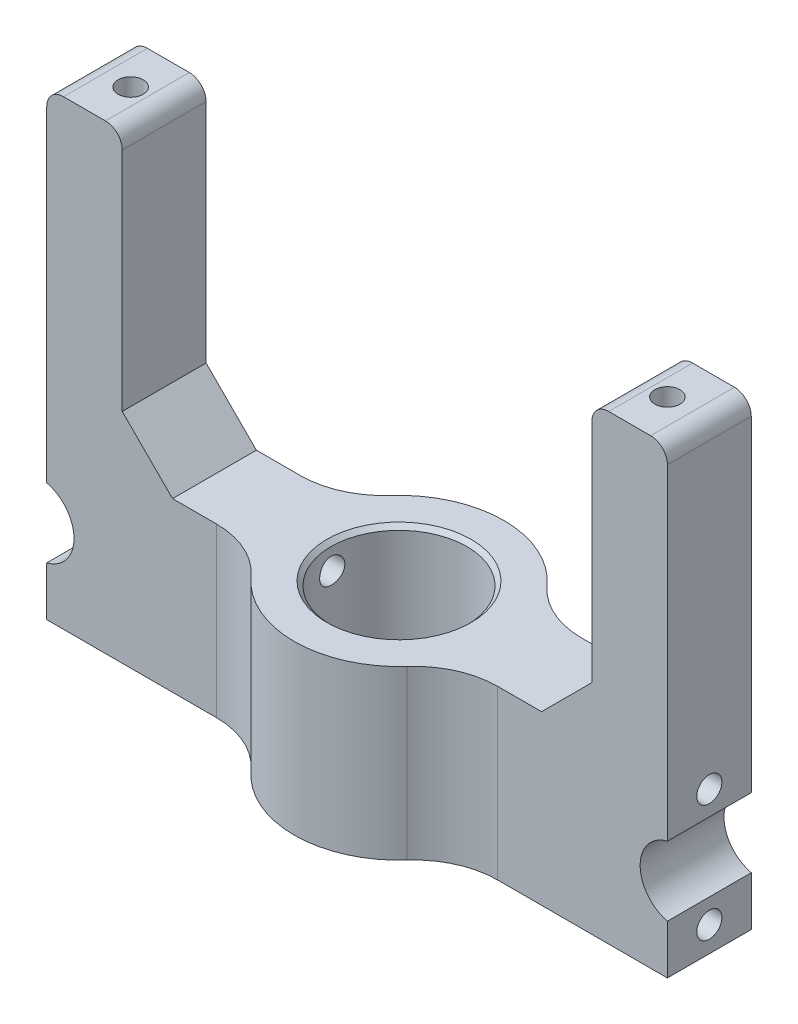
SolidWorks part; units mm, degrees
ref_plane "Front Plane" through (0, 0, 0) normal (0, 0, 1) x (1, 0, 0)
ref_plane "Top Plane" through (0, 0, 0) normal (0, 1, 0) x (1, 0, 0)
ref_plane "Right Plane" through (0, 0, 0) normal (1, 0, 0) x (0, 0, -1)
sketch "Sketch1" plane through (0, 0, 0) normal (0, 1, 0) x (1, 0, 0)
  line L0 (-44, 0) -> (-44, -44) construction
  line L1 (-44, -44) -> (44, -44) construction
  line L2 (44, -44) -> (44, 0) construction
  line L4 (-44, -5) -> (44, -5)
  line L5 (-44, -5) -> (-44, 5)
  line L6 (-44, 5) -> (44, 5)
  line L7 (44, -5) -> (44, 5)
  line L8 (-44, -5) -> (44, 5) construction
  line L9 (-44, 5) -> (44, -5) construction
  arc A0 (44, 0) -> (-44, 0) centre (0, 0) ccw construction
  dimension "D1" = 88
  dimension "D2" = 88
  dimension "D3" = 10
extrude "Boss-Extrude1" add sketch "Sketch1" along normal blind 20
sketch "Sketch2" plane through (0, 0, 5) normal (0, 0, 1) x (1, 0, 0)
  line L1 (-1044, 10) -> (48956, 10) construction
  line L2 (0, -1000) -> (0, 49000) construction
  line L3 (-44, 20) -> (-44, 0) construction
  circle A0 centre (-38, 10) radius 4.25
  circle A1 centre (38, 10) radius 4.25
  point P2 (-44, 10)
  dimension "D1" = 8.5
  dimension "D2" = 6
extrude "Cut-Extrude1" cut sketch "Sketch2" against normal through all
sketch "Sketch7" plane through (0, 20, 0) normal (0, 1, 0) x (1, 0, 0)
  circle A0 centre (0, 0) radius 12.5
  dimension "D1" = 25
extrude "Boss-Extrude2" add sketch "Sketch7" against normal up to surface (20 mm away) up to face at (0, 0, 0)
sketch "Sketch4" plane through (0, 20, 0) normal (0, 1, 0) x (1, 0, 0)
  circle A0 centre (0, 0) radius 8.1
  dimension "D1" = 16.2
extrude "Cut-Extrude3" cut sketch "Sketch4" against normal through all
fillet "Fillet2" radius 10 4 edges at (-11.4564, 10, 5) (11.4564, 10, 5) (11.4564, 10, -5) (-11.4564, 10, -5)
sketch "Sketch9" plane through (0, 0, 5) normal (0, 0, 1) x (1, 0, 0)
  line L0 (-44, 0) -> (-16.7705, 0) construction
  line L1 (-44, 20) -> (-37, 20)
  line L2 (-44, 20) -> (-44, 0)
  line L3 (-44, 0) -> (-37, 0)
  line L4 (-37, 20) -> (-37, 0)
  line L5 (16.7705, 0) -> (44, 0) construction
  line L6 (44, 20) -> (37, 20)
  line L7 (44, 20) -> (44, 0)
  line L8 (44, 0) -> (37, 0)
  line L9 (37, 20) -> (37, 0)
  point P14 (38, 10)
  dimension "D1" = 1
extrude "Cut-Extrude6" cut sketch "Sketch9" against normal through all
sketch "Sketch10" plane through (0, 20, 0) normal (0, 1, 0) x (1, 0, 0)
  line L0 (-37, -5) -> (-16.7705, -5) construction
  line L1 (-37, 5) -> (-28, 5)
  line L2 (-37, 5) -> (-37, -5)
  line L3 (-37, -5) -> (-28, -5)
  line L4 (-28, 5) -> (-28, -5)
  dimension "D1" = 28
extrude "Boss-Extrude3" add sketch "Sketch10" along normal blind 35
sketch "Sketch11" plane through (0, 55, 0) normal (0, 1, 0) x (1, 0, 0)
  circle A0 centre (-32, 0) radius 1.5
  point P2 (0, 0)
  dimension "D1" = 3
  dimension "D2" = 32
extrude "Cut-Extrude7" cut sketch "Sketch11" against normal blind 20
chamfer "Chamfer1" distance 6 angle 45 1 edges at (-28, 20, 0)
fillet "Fillet3" radius 2 2 edges at (-37, 55, 0) (-28, 55, 0)
mirror "Mirror1" about plane through (0, 0, 0) normal (1, 0, 0) of "Chamfer1", "Cut-Extrude7", "Boss-Extrude3", "Fillet3"
chamfer "Chamfer2" distance 0.5 angle 45 2 edges at (0, 0, 8.1) (0, 20, 8.1)
sketch "Sketch12" plane through (-37, 0, 0) normal (-1, 0, 0) x (0, 0, 1)
  line L4 (-995, 10) -> (49005, 10) construction
  line L5 (5, 5.8693) -> (5, 14.1307) construction
  line L6 (-5, 0) -> (-5, 5.8693) construction
  circle A0 centre (0, 3) radius 1.5
  circle A1 centre (0, 17) radius 1.5
  point P4 (-5, 2.9347)
  point P13 (5, 10)
  dimension "D1" = 3
  dimension "D2" = 3
  dimension "D3" = 7
  dimension "D4" = 7
extrude "Cut-Extrude8" cut sketch "Sketch12" against normal through all
